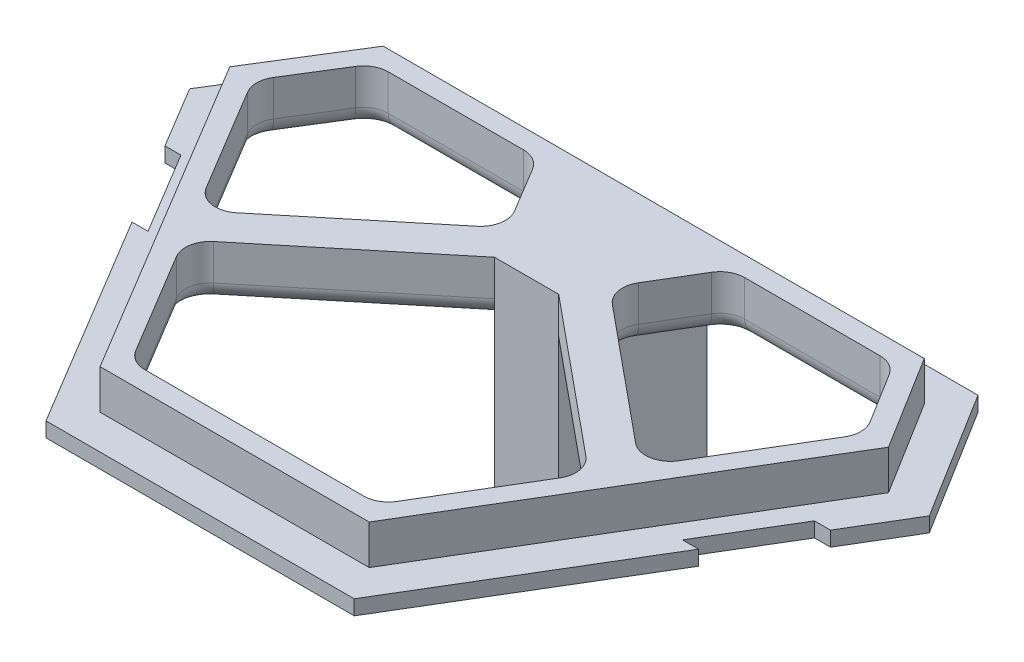
SolidWorks part; units mm, degrees
ref_plane "Front" through (0, 0, 0) normal (0, 0, 1) x (1, 0, 0)
ref_plane "Top" through (0, 0, 0) normal (0, 1, 0) x (1, 0, 0)
ref_plane "Right" through (0, 0, 0) normal (1, 0, 0) x (0, 0, -1)
sketch "Sketch1" plane through (0, 0, 0) normal (0, 1, 0) x (1, 0, 0)
  line L0 (12.5, -19.497) -> (22.9775, -2.0445)
  line L1 (22.9775, -2.0445) -> (21.6775, -2.0445)
  line L2 (21.6775, -2.0445) -> (25.6922, 4.6429)
  line L3 (25.6922, 4.6429) -> (26.9922, 4.6429)
  line L4 (26.9922, 4.6429) -> (30, 9.653)
  line L5 (-21.0551, 15.703) -> (21.0551, 15.703)
  line L6 (30, 9.653) -> (23.5, 20.103)
  line L7 (-23.5, 20.103) -> (23.5, 20.103)
  line L10 (-23.5, 20.103) -> (-30, 9.653)
  line L11 (-30, 9.653) -> (-26.9922, 4.6429)
  line L12 (-25.6922, 4.6429) -> (-26.9922, 4.6429)
  line L13 (-10.0095, -15.097) -> (10.0095, -15.097)
  line L14 (-25.6922, 4.6429) -> (-21.6775, -2.0445)
  line L15 (-21.6775, -2.0445) -> (-22.9775, -2.0445)
  line L16 (-22.9775, -2.0445) -> (-12.5, -19.497)
  line L17 (-12.5, -19.497) -> (12.5, -19.497)
  line L18 (10.0095, -15.097) -> (24.8436, 9.6123)
  line L27 (24.8436, 9.6123) -> (21.0551, 15.703)
  line L31 (-21.0551, 15.703) -> (-24.8436, 9.6123)
  line L32 (-24.8436, 9.6123) -> (-10.0095, -15.097)
extrude "Boss-Extrude1" add sketch "Sketch1" along normal blind 1.2
sketch "Sketch2" plane through (0, 1.2, 0) normal (0, 1, 0) x (1, 0, 0)
  line L27 (26.7186, 9.6271) -> (21.9442, 17.303)
  line L28 (10.9151, -16.697) -> (26.7186, 9.6271)
  line L29 (-10.9151, -16.697) -> (10.9151, -16.697)
  line L30 (-26.7186, 9.6271) -> (-10.9151, -16.697)
  line L31 (21.9442, 17.303) -> (-21.9442, 17.303)
  line L32 (-21.9442, 17.303) -> (-26.7186, 9.6271)
  line L33 (26.7186, 9.6271) -> (21.9442, 17.303)
  line L34 (10.9151, -16.697) -> (26.7186, 9.6271)
  line L35 (-10.9151, -16.697) -> (10.9151, -16.697)
  line L36 (-26.7186, 9.6271) -> (-10.9151, -16.697)
  line L37 (21.9442, 17.303) -> (-21.9442, 17.303)
  line L38 (-21.9442, 17.303) -> (-26.7186, 9.6271)
  line L60 (24.8436, 9.6123) -> (21.0551, 15.703)
  line L61 (21.0551, 15.703) -> (-21.0551, 15.703)
  line L62 (-21.0551, 15.703) -> (-24.8436, 9.6123)
  line L63 (-24.8436, 9.6123) -> (-10.0095, -15.097)
  line L64 (-10.0095, -15.097) -> (10.0095, -15.097)
  line L65 (10.0095, -15.097) -> (24.8436, 9.6123)
  line L66 (24.8436, 9.6123) -> (21.0551, 15.703)
  line L67 (21.0551, 15.703) -> (-21.0551, 15.703)
  line L68 (-21.0551, 15.703) -> (-24.8436, 9.6123)
  line L69 (-24.8436, 9.6123) -> (-10.0095, -15.097)
  line L70 (-10.0095, -15.097) -> (10.0095, -15.097)
  line L71 (10.0095, -15.097) -> (24.8436, 9.6123)
  dimension "D1" = 1.6
  dimension "D2" = 0
extrude "Boss-Extrude2" add sketch "Sketch2" along normal blind 4.2
sketch "Sketch3" plane through (0, 0, 0) normal (0, -1, 0) x (1, 0, 0)
  line L0 (0, 0) -> (0, -13) construction
  line L2 (2.6028, -6.9864) -> (2.6028, -19.0136)
  line L3 (2.6028, -19.0136) -> (-2.6028, -19.0136)
  line L4 (-2.6028, -19.0136) -> (-2.6028, -6.9864)
  line L5 (-2.6028, -6.9864) -> (2.6028, -6.9864)
  point P6 (0, -13)
  point P9 (2.6028, -13)
extrude "Boss-Extrude3" add sketch "Sketch3" along normal blind 14
chamfer "Chamfer3" distance 1 angle 45 1 edges at (0, 0, -19.0136)
sketch "Sketch4" plane through (0, 0, 0) normal (0, 1, 0) x (1, 0, 0)
  line L8 (2.6028, 6.9864) -> (2.6028, 15.703)
  line L9 (2.6028, 15.703) -> (-2.6028, 15.703)
  line L10 (-2.6028, 15.703) -> (-2.6028, 6.9864)
  line L11 (-2.6028, 6.9864) -> (2.6028, 6.9864)
  line L12 (2.6028, 6.9864) -> (2.6028, 15.703)
  line L13 (2.6028, 15.703) -> (-2.6028, 15.703)
  line L14 (-2.6028, 15.703) -> (-2.6028, 6.9864)
  line L15 (-2.6028, 6.9864) -> (2.6028, 6.9864)
  dimension "D1" = 0
extrude "Boss-Extrude4" add sketch "Sketch4" along normal up to surface (5.4 mm away) up to face at (0, 5.4, -3.411)
sketch "Sketch6" plane through (0, 5.4, 0) normal (0, 1, 0) x (1, 0, 0)
  line L0 (2.6028, 6.9864) -> (2.6028, 15.703)
  line L1 (-2.6028, 6.9864) -> (-17.7925, -2.1327) construction
  line L2 (-24.8436, 9.6123) -> (-10.0095, -15.097) construction
  line L3 (-2.6028, 6.9864) -> (-7.8358, 15.703)
  line L4 (-2.6028, 15.703) -> (-21.0551, 15.703) construction
  line L5 (-7.8358, 15.703) -> (-2.6028, 15.703)
  line L6 (-2.6028, 15.703) -> (-2.6028, 6.9864)
  line L7 (-7.8358, 15.703) -> (-2.6028, 15.703)
  line M12 (-21.0551, 15.703) -> (-2.6028, 15.703)
  line M13 (-2.6028, 15.703) -> (-2.6028, 6.9864)
extrude "Boss-Extrude5" add sketch "Sketch6" against normal up to surface (5.4 mm away) contours L3 M13 M12 up to face at (0, 0, -2.208)
mirror "Mirror1" about plane through (0, 0, 0) normal (1, 0, 0) of "Boss-Extrude5"
sketch "Sketch10" plane through (0, 0, 0) normal (0, -1, 0) x (-1, 0, 0)
  line L0 (-2.6028, 6.9864) -> (-4.147, 9.5585)
  line L1 (-7.8358, 15.703) -> (-2.6028, 6.9864) construction
  line L2 (-4.147, 9.5585) -> (-17.9765, -1.8263)
  line L3 (-10.0095, -15.097) -> (-24.8436, 9.6123) construction
  line L4 (-17.9765, -1.8263) -> (-16.4323, -4.3984)
  line L5 (-16.4323, -4.3984) -> (-2.6028, 6.9864)
  line L8 (24.8436, 9.6123) -> (10.0095, -15.097) construction
  line L9 (2.6028, 6.9864) -> (4.147, 9.5585)
  line L10 (7.8358, 15.703) -> (2.6028, 6.9864) construction
  line L11 (2.6028, 6.9864) -> (16.4323, -4.3984)
  line L12 (16.4323, -4.3984) -> (17.9765, -1.8263)
  line L13 (17.9765, -1.8263) -> (4.147, 9.5585)
extrude "Boss-Extrude8" add sketch "Sketch10" against normal up to surface (5.4 mm away) up to face at (0, 5.4, -6.5815)
fillet "Fillet1" radius 2 14 edges at (-16.4323, 2.7, 4.3984) (16.4323, 2.7, 4.3984) (10.0095, 2.7, 15.097) (-10.0095, 2.7, 15.097) (-21.0551, 2.7, -15.703) (-24.8436, 2.7, -9.6123) (-17.9765, 2.7, 1.8263) (-7.8358, 2.7, -15.703) (7.8358, 2.7, -15.703) (21.0551, 2.7, -15.703) (24.8436, 2.7, -9.6123) (17.9765, 2.7, 1.8263) (4.147, 2.7, -9.5585) (-4.147, 2.7, -9.5585)
fillet "Fillet3" radius 1.4835 29 edges at (-17.7958, 0, 0.7783) (-21.6927, 0, -4.3638) (-24.4997, 0, -9.6096) (-22.92, 0, -12.7048) (-20.9152, 0, -15.4512) (-14.4558, 0, -15.703) (-7.9827, 0, -15.4435) (-6.1437, 0, -12.8844) (-4.778, 0, -9.6672) (-8.8522, 0, -1.8418) (-15.8013, 0, 4.5071) (-13.0686, 0, 10.0013) (-9.8626, 0, 14.8375) (0, 0, 15.097) (9.8626, 0, 14.8375) (13.0686, 0, 10.0013) (15.8013, 0, 4.5071) (4.778, 0, -9.6672) (6.1437, 0, -12.8844) (7.9827, 0, -15.4435) (14.4558, 0, -15.703) (20.9152, 0, -15.4512) (22.92, 0, -12.7048) (24.4997, 0, -9.6096) (21.6927, 0, -4.3638) (17.7958, 0, 0.7783) (-10.8314, 0, -4.0557) (8.8522, 0, -1.8418) (10.8314, 0, -4.0557)
sketch "Sketch12" plane through (0, 5.4, 0) normal (0, 1, 0) x (1, 0, 0)
  circle A0 centre (0, 0) radius 31.5014
extrude "Cut-Extrude1" cut sketch "Sketch12" against normal blind 1
